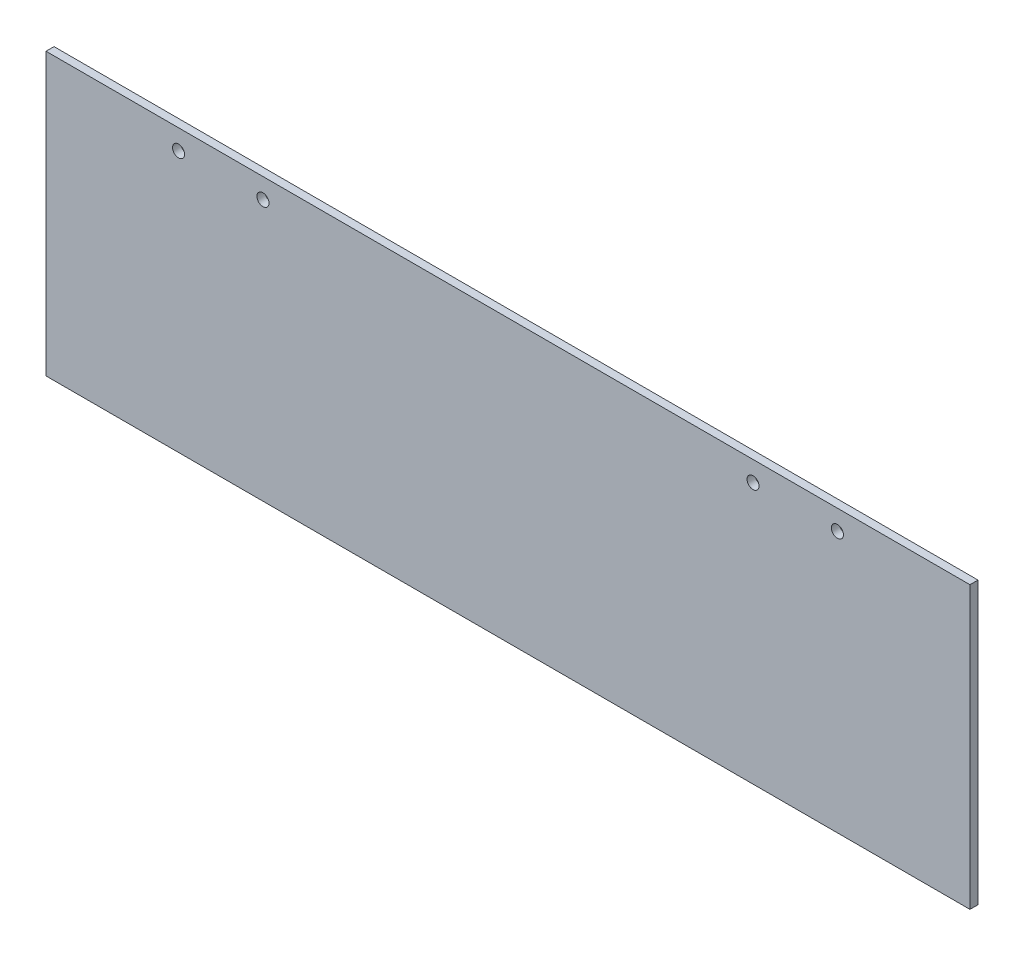
SolidWorks part; units mm, degrees
ref_plane "Plan de face" through (0, 0, 0) normal (0, 0, 1) x (1, 0, 0)
ref_plane "Plan de dessus" through (0, 0, 0) normal (0, 1, 0) x (1, 0, 0)
ref_plane "Plan de droite" through (0, 0, 0) normal (1, 0, 0) x (0, 0, -1)
sketch "Esquisse1" plane through (0, 0, 0) normal (0, 0, 1) x (1, 0, 0)
  line L1 (-115, 35) -> (115, 35)
  line L2 (-115, 35) -> (-115, -35)
  line L3 (-115, -35) -> (115, -35)
  line L4 (115, 35) -> (115, -35)
  circle A0 centre (-82, 30) radius 1.5
  circle A1 centre (-61, 30) radius 1.5
  circle A2 centre (61, 30) radius 1.5
  circle A3 centre (82, 30) radius 1.5
  dimension "D11" = 3
  dimension "D12" = 3
  dimension "D13" = 3
  dimension "D14" = 3
  dimension "D1" = 230
  dimension "D2" = 115
  dimension "D3" = 70
  dimension "D4" = 35
  dimension "D5" = 5
  dimension "D6" = 5
  dimension "D7" = 5
  dimension "D8" = 5
  dimension "D9" = 21
  dimension "D10" = 21
  dimension "D15" = 61
  dimension "D16" = 61
extrude "Boss.-Extru.1" add sketch "Esquisse1" along normal blind 2
